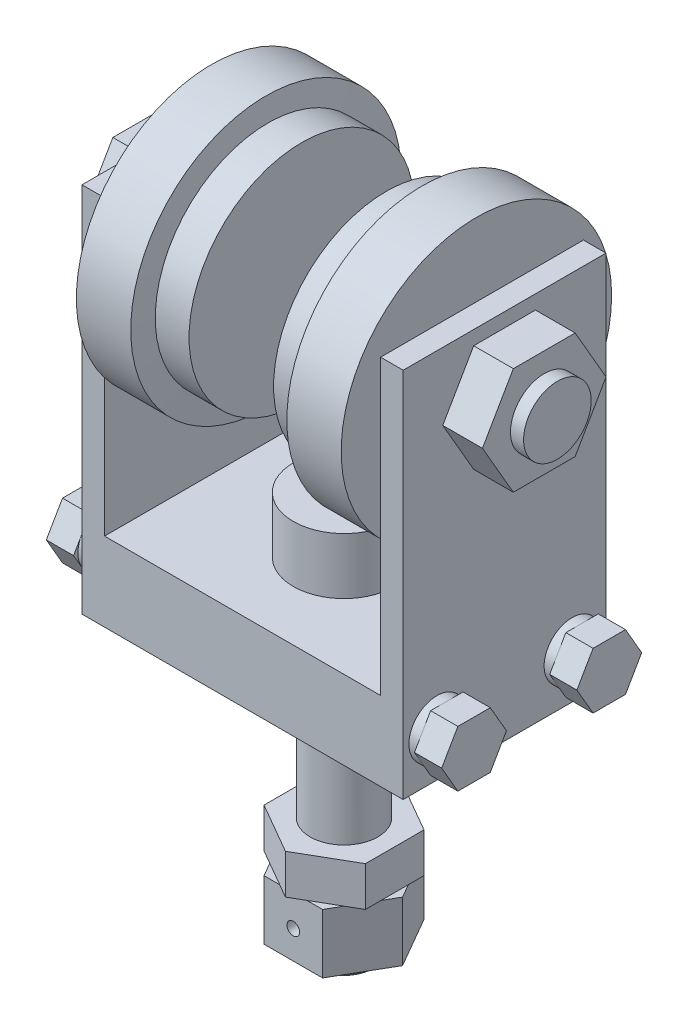
SolidWorks part; units mm, degrees
ref_plane "Front" through (0, 0, 0) normal (0, 0, 1) x (1, 0, 0)
ref_plane "Top" through (0, 0, 0) normal (0, 1, 0) x (1, 0, 0)
ref_plane "Right" through (0, 0, 0) normal (1, 0, 0) x (0, 0, -1)
ref_plane "Z PLANE" through (0, 0, 0) normal (0, 0, 1) x (1, 0, 0)
ref_plane "YOKE BOTTOM" through (0, 0, 0) normal (0, 1, 0) x (-1, 0, 0)
ref_plane "X PLANE" through (0, 0, 0) normal (1, 0, 0) x (0, 0, -1)
sketch "YOKE CROSS SECTION" plane through (0, 0, 0) normal (1, 0, 0) x (0, 0, -1)
  line L0 (0, 0) -> (0, 57.0916) construction
  line L1 (0, 84.8167) -> (0, -84.8167) construction
  line L2 (-57.15, 0) -> (57.15, 0)
  line L3 (69.1602, 0) -> (-69.1602, 0) construction
  line L4 (57.15, 0) -> (57.15, 44.45)
  line L5 (-57.15, 0) -> (-57.15, 44.45)
  line L6 (57.15, 44.45) -> (-57.15, 44.45)
  point P12 (0, 44.45)
  dimension "D1" = 44.45
  dimension "D2" = 114.3
ref_plane "1/2 YOKE LENGTH (A)" through (77.7875, 0, 0) normal (1, 0, 0) x (0, 0, -1)
extrude "YOKE" add sketch "YOKE CROSS SECTION" along normal up to surface (77.7875 mm away) up to plane "1/2 YOKE LENGTH (A)"
sketch "SIDEPLATE PROFILE" plane through (77.7875, 0, 0) normal (1, 0, 0) x (0, 0, -1)
  line L0 (0, 0) -> (0, 74.7424) construction
  line L1 (0, 84.8167) -> (0, -84.8167) construction
  line L2 (-57.15, 0) -> (57.15, 0)
  line L3 (57.15, 0) -> (57.15, 209.55)
  line L4 (-57.15, 0) -> (-57.15, 209.55)
  line L5 (57.15, 209.55) -> (-57.15, 209.55)
  point P11 (0, 209.55)
  dimension "D1" = 209.55
ref_plane "WHEEL HEIGHT" through (0, 171.45, 0) normal (0, 1, 0) x (-1, 0, 0)
ref_plane "SCREW LOCATION X" through (0, 0, 38.1) normal (0, 0, 1) x (1, 0, 0)
ref_plane "SCREW LOCATION Y" through (0, 25.4, 0) normal (0, 1, 0) x (-1, 0, 0)
extrude "SIDEPLATE" add sketch "SIDEPLATE PROFILE" along normal blind 12.7
sketch "WHEEL PIN NUT PROFILE" plane through (90.4875, 0, 0) normal (1, 0, 0) x (0, 0, -1)
  line L0 (0, 84.8167) -> (0, -84.8167) construction
  line L1 (34.8287, 171.45) -> (17.4143, 201.6125)
  line L2 (17.4143, 201.6125) -> (-17.4143, 201.6125)
  line L3 (-17.4143, 201.6125) -> (-34.8287, 171.45)
  line L4 (-34.8287, 171.45) -> (-17.4143, 141.2875)
  line L5 (-17.4143, 141.2875) -> (17.4143, 141.2875)
  line L6 (17.4143, 141.2875) -> (34.8287, 171.45)
  line L7 (69.1602, 171.45) -> (-69.1602, 171.45) construction
  circle A0 centre (0, 171.45) radius 30.1625 construction
  dimension "D1" = 60.325
extrude "WHEEL PIN NUT" add sketch "WHEEL PIN NUT PROFILE" along normal blind 22.352
sketch "WHEEL PIN PROJECTION PROFILE" plane through (112.8395, 0, 0) normal (1, 0, 0) x (0, 0, -1)
  line L0 (0, 84.8167) -> (0, -84.8167) construction
  line L1 (69.1602, 171.45) -> (-69.1602, 171.45) construction
  circle A0 centre (0, 171.45) radius 19.05
  dimension "D1" = 38.1
extrude "WHEEL PIN PROJECTION" add sketch "WHEEL PIN PROJECTION PROFILE" along normal blind 7.4168
sketch "LOCKNUTS PROFILE" plane through (90.4875, 0, 0) normal (1, 0, 0) x (0, 0, -1)
  line L0 (-38.1, 84.8167) -> (-38.1, -84.8167) construction
  line L1 (50, 25.4) -> (-50, 25.4) construction
  circle A0 centre (-38.1, 25.4) radius 15.8115
  dimension "D1" = 31.623
extrude "LOCKNUTS" add sketch "LOCKNUTS PROFILE" along normal blind 5.5626
sketch "SCREWS PROFILE" plane through (96.0501, 0, 0) normal (1, 0, 0) x (0, 0, -1)
  line L0 (50, 25.4) -> (-50, 25.4) construction
  line L1 (-19.8425, 25.4) -> (-28.9712, 41.2115)
  line L2 (-28.9712, 41.2115) -> (-47.2288, 41.2115)
  line L3 (-47.2288, 41.2115) -> (-56.3575, 25.4)
  line L4 (-56.3575, 25.4) -> (-47.2288, 9.5885)
  line L5 (-47.2288, 9.5885) -> (-28.9712, 9.5885)
  line L6 (-28.9712, 9.5885) -> (-19.8425, 25.4)
  line L7 (-38.1, 84.8167) -> (-38.1, -84.8167) construction
  circle A0 centre (-38.1, 25.4) radius 15.8115 construction
  dimension "D1" = 31.623
extrude "SCREWS" add sketch "SCREWS PROFILE" along normal blind 15.3416
sketch "PROFILE" plane through (0, 44.45, 0) normal (0, 1, 0) x (-1, 0, 0)
  line L0 (84.8167, 0) -> (-84.8167, 0) construction
  line L1 (0, 83.2389) -> (0, -83.2389) construction
  circle A0 centre (0, 0) radius 28.575
  dimension "D1" = 57.15
extrude "KING BOLT HEAD" add sketch "PROFILE" along normal blind 31.75
mirror "Mirror1" about plane through (0, 0, 0) normal (0, 0, 1) of "SCREWS", "LOCKNUTS"
mirror "Mirror5" about plane through (0, 0, 0) normal (1, 0, 0) of bodies 112
ref_plane "TOP OF NUT" through (0, -82.55, 0) normal (0, 1, 0) x (-1, 0, 0)
sketch "DIA." plane through (0, 0, 0) normal (0, -1, 0) x (1, 0, 0)
  line L0 (84.8167, 0) -> (-84.8167, 0) construction
  line L1 (0, -83.2389) -> (0, 83.2389) construction
  circle A0 centre (0, 0) radius 19.05
  dimension "D1" = 38.1
extrude "KING BOLT" add sketch "DIA." along normal up to surface (82.55 mm away) up to plane "TOP OF NUT"
sketch "KING BOLT JAN NUT PROFILE" plane through (0, -82.55, 0) normal (0, -1, 0) x (1, 0, 0)
  line L0 (84.8167, 0) -> (-84.8167, 0) construction
  line L1 (0, -32.9956) -> (28.575, -16.4978)
  line L2 (28.575, -16.4978) -> (28.575, 16.4978)
  line L3 (28.575, 16.4978) -> (0, 32.9956)
  line L4 (0, 32.9956) -> (-28.575, 16.4978)
  line L5 (-28.575, 16.4978) -> (-28.575, -16.4978)
  line L6 (-28.575, -16.4978) -> (0, -32.9956)
  line L7 (0, -83.2389) -> (0, 83.2389) construction
  circle A0 centre (0, 0) radius 28.575 construction
  dimension "D1" = 57.15
extrude "KING BOLT JAM NUT" add sketch "KING BOLT JAN NUT PROFILE" along normal blind 22.352
sketch "KING BOLT NUT PROFILE" plane through (0, -104.902, 0) normal (0, -1, 0) x (1, 0, 0)
  line L1 (32.9956, 0) -> (16.4978, 28.575)
  line L2 (16.4978, 28.575) -> (-16.4978, 28.575)
  line L3 (-16.4978, 28.575) -> (-32.9956, 0)
  line L4 (-32.9956, 0) -> (-16.4978, -28.575)
  line L5 (-16.4978, -28.575) -> (16.4978, -28.575)
  line L6 (16.4978, -28.575) -> (32.9956, 0)
  line L10 (0, -83.2389) -> (0, 83.2389) construction
  line L11 (84.8167, 0) -> (-84.8167, 0) construction
  circle A0 centre (0, 0) radius 28.575 construction
  dimension "D1" = 57.15
extrude "KING BOLT NUT" add sketch "KING BOLT NUT PROFILE" along normal blind 33.4518
sketch "Sketch5" plane through (0, -138.3538, 0) normal (0, -1, 0) x (1, 0, 0)
  circle A0 centre (0, 0) radius 19.05 construction
  circle A1 centre (0, 0) radius 19.05
extrude "EXTENDED KING BOLT" add sketch "Sketch5" along normal blind 9.525
chamfer "Chamfer1" distance 2.3812 angle 45 1 edges at (0, -147.8788, -19.05)
ref_plane "MOUNTING REF PLANE" through (0, -34.925, 0) normal (0, 1, 0) x (-1, 0, 0)
sketch "Sketch6" plane through (0, 0, 0) normal (0, 0, 1) x (1, 0, 0)
  line L0 (42.8625, 234.95) -> (23.8125, 234.95)
  line L1 (23.8125, 171.45) -> (77.7875, 171.45)
  line L2 (23.8125, 171.45) -> (23.8125, 234.95)
  line L3 (74.6125, 247.65) -> (74.6125, 198.0848)
  line L4 (77.7875, 171.45) -> (77.7875, 198.0848)
  line L5 (77.7875, 198.0848) -> (74.6125, 198.0848)
  line L6 (42.8625, 234.95) -> (43.9736, 247.65)
  line L7 (43.9736, 247.65) -> (74.6125, 247.65)
  line L8 (69.1602, 171.45) -> (-69.1602, 171.45) construction
  line L11 (77.7875, -75.0522) -> (77.7875, 75.0522) construction
  dimension "D1" = 26.6348
  dimension "D2" = 76.2
  dimension "D3" = 63.5
  dimension "D4" = 3.175
  dimension "D5" = 33.8139
  dimension "D6" = 53.975
  dimension "D7" = 34.925
  dimension "D8" = 3.175
revolve "WHEEL" add sketch "Sketch6" angle 360 about axis through (120.2563, 171.45, 0) along (-1, 0, 0)
mirror "Mirror6" about plane through (0, 0, 0) normal (1, 0, 0) of "WHEEL"
sketch "Sketch7" plane through (0, 0, 28.575) normal (0, 0, 1) x (1, 0, 0)
  line L0 (0, -83.2389) -> (0, 83.2389) construction
  line L1 (-16.4978, -138.3538) -> (-32.9956, -138.3538) construction
  circle A0 centre (0, -122.4788) radius 3.5719
  dimension "D1" = 7.1437
  dimension "D2" = 15.875
extrude "COTTER PIN HOLE" cut sketch "Sketch7" against normal up to next
sketch "Sketch8" plane through (0, 0, 0) normal (0, -1, 0) x (1, 0, 0)
  circle A0 centre (0, 0) radius 25.4
  circle A1 centre (0, 0) radius 30.1625
  dimension "D1" = 50.8
  dimension "D2" = 60.325
extrude "SPACER" [suppressed] add sketch "Sketch8" along normal blind 12.7
ref_plane "TREAD OF TRACK" through (0, 107.95, 0) normal (0, 1, 0) x (-1, 0, 0)
